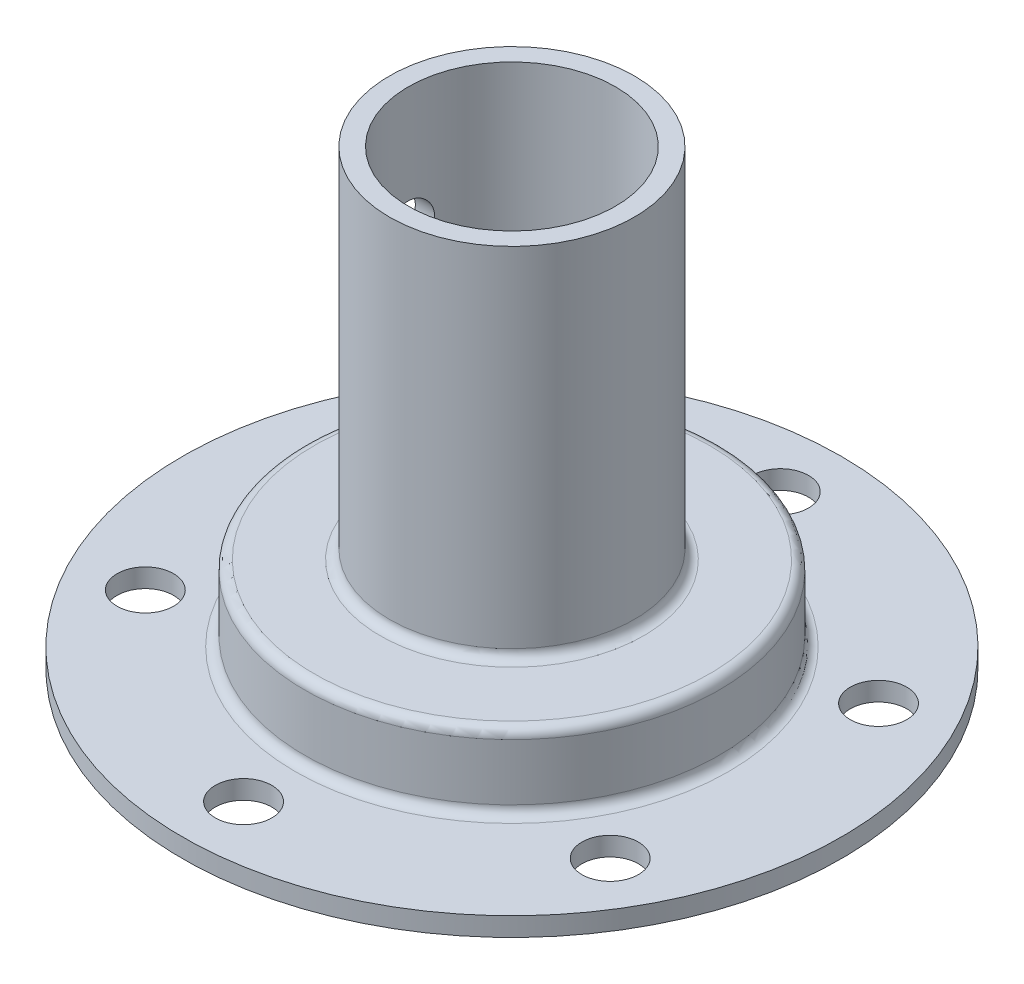
SolidWorks part; units mm, degrees
material "1060 合金"
ref_plane "前视基准面" through (0, 0, 0) normal (0, 0, 1) x (1, 0, 0)
ref_plane "上视基准面" through (0, 0, 0) normal (0, 1, 0) x (1, 0, 0)
ref_plane "右视基准面" through (0, 0, 0) normal (1, 0, 0) x (0, 0, -1)
sketch "草图1" plane through (0, 0, 0) normal (0, 0, 1) x (1, 0, 0)
  line L0 (0, 0) -> (0, 81.5505) construction
  line L3 (20, 0) -> (35, 0)
  line L4 (35, 0) -> (35, 2)
  line L5 (35, 2) -> (23, 2)
  line L6 (22, 3) -> (22, 9)
  line L7 (21, 10) -> (14, 10)
  line L8 (13, 11) -> (13, 48)
  line L9 (13, 48) -> (11, 48)
  line L10 (11, 48) -> (11, 8)
  line L11 (11, 8) -> (19, 8)
  line L12 (20, 7) -> (20, 0)
  arc A0 (23, 2) -> (22, 3) centre (23, 3) cw
  arc A1 (19, 8) -> (20, 7) centre (19, 7) cw
  arc A2 (22, 9) -> (21, 10) centre (21, 9) ccw
  arc A3 (14, 10) -> (13, 11) centre (14, 11) cw
  dimension "D9" = 1
  dimension "D2" = 2
  dimension "D3" = 2
  dimension "D4" = 2
  dimension "D5" = 13
  dimension "D6" = 2
  dimension "D7" = 40
  dimension "D8" = 10
  dimension "D10" = 20
  dimension "D11" = 35
revolve "旋转1" add sketch "草图1" angle 360 about L0
sketch "草图2" plane through (0, 2, 0) normal (0, 1, 0) x (1, 0, 0)
  circle A0 centre (0, 28.5) radius 3
  circle A1 centre (24.6817, 14.25) radius 3
  circle A2 centre (24.6817, -14.25) radius 3
  circle A3 centre (0, -28.5) radius 3
  circle A4 centre (-24.6817, -14.25) radius 3
  circle A5 centre (-24.6817, 14.25) radius 3
  point P15 (0, 0)
  dimension "D1" = 28.5
  dimension "D3" = 6
  dimension "D2" = 6
extrude "切除-拉伸1" cut sketch "草图2" against normal through all
sketch "草图3" plane through (0, 0, 0) normal (1, 0, 0) x (0, 0, -1)
  line L0 (0, 10) -> (0, 35) construction
  line L1 (21, 10) -> (-21, 10) construction
  circle A0 centre (0, 35) radius 2.5
  dimension "D1" = 25
  dimension "D2" = 5
extrude "切除-拉伸2" cut sketch "草图3" against normal through all
equation "\"32。5\"=55"
